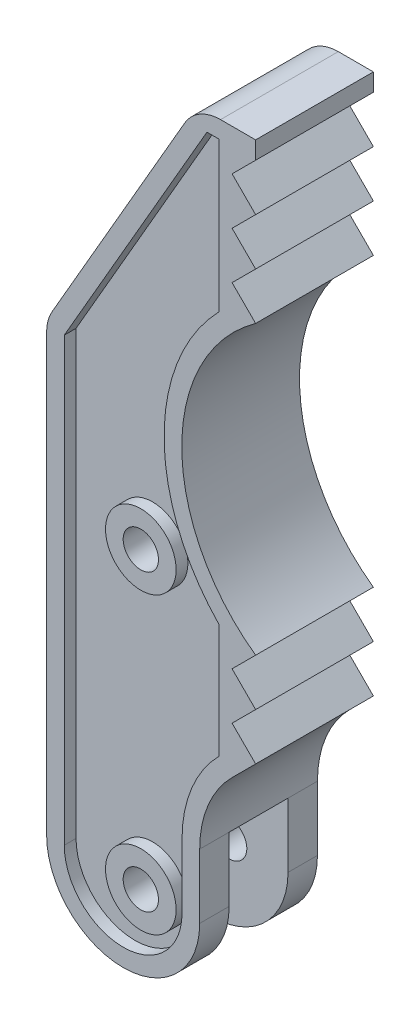
SolidWorks part; units mm, degrees
ref_plane "Front Plane" through (0, 0, 0) normal (0, 0, 1) x (1, 0, 0)
ref_plane "Top Plane" through (0, 0, 0) normal (0, 1, 0) x (1, 0, 0)
ref_plane "Right Plane" through (0, 0, 0) normal (1, 0, 0) x (0, 0, -1)
sketch "Sketch1" plane through (0, 0, 0) normal (0, 0, 1) x (1, 0, 0)
  line L0 (0, 0) -> (0, 60) construction
  line L1 (0, 60) -> (-5, 60) construction
  line L2 (-5, 60) -> (-17.75, 37.9164) construction
  line L3 (-17.75, 37.9164) -> (-17.75, 0) construction
  line L4 (-17.75, 0) -> (0, 0) construction
  line L5 (0, 58.5) -> (-2, 56.5)
  line L6 (-2, 60) -> (0, 60) construction
  line L7 (-2, 60) -> (-2, 45) construction
  line L8 (-2, 45) -> (0, 45) construction
  line L9 (0, 60) -> (0, 45) construction
  line L10 (-2, 56.5) -> (0, 54.5)
  line L11 (0, 54.5) -> (-2, 52.5)
  line L12 (-2, 52.5) -> (0, 50.5)
  line L13 (0, 50.5) -> (-2, 48.5)
  line L14 (-2, 48.5) -> (0, 46.5)
  line L15 (-17.75, 34.3) -> (0, 34.3) construction
  line L16 (-2, 20.1) -> (0, 22.1)
  line L17 (0, 18.1) -> (-2, 20.1)
  line L18 (-2, 16.1) -> (0, 18.1)
  line L19 (0, 14.1) -> (-2, 16.1)
  line L20 (-2, 12.1) -> (0, 14.1)
  line L21 (0, 58.5) -> (0, 60)
  line L22 (0, 60) -> (-5, 60)
  line L23 (-5, 60) -> (-17.75, 37.9164)
  line L24 (-17.75, 37.9164) -> (-17.75, 0)
  line L25 (-4.75, 0) -> (-4.75, 5.4609)
  line L26 (-9.75, 0) -> (-9.75, 25) construction
  arc A0 (0, 46.5) -> (0, 22.1) centre (8.727, 34.3) ccw
  arc A1 (-17.75, 0) -> (-4.75, 0) centre (-11.25, 0) ccw
  arc A2 (-4.75, 5.4609) -> (-2, 12.1) centre (4.6391, 5.4609) cw
  circle A3 centre (-9.75, 0) radius 1.5
  circle A4 centre (-9.75, 25) radius 1.5
  dimension "D10" = 15
  dimension "D11" = 6.5
  dimension "D12" = 3
  dimension "D1" = 60
  dimension "D2" = 5
  dimension "D3" = 30
  dimension "D4" = 17.75
  dimension "D5" = 2
  dimension "D6" = 15
  dimension "D7" = 1.5
  dimension "D8" = 3.5
  dimension "D9" = 24.2
  dimension "D13" = 5
  dimension "D14" = 25
extrude "Boss-Extrude1" add sketch "Sketch1" along normal mid plane 10
sketch "Sketch3" plane through (0, 0, 0) normal (0, 0, 1) x (1, 0, 0)
  line L1 (-15, -38.4108) -> (-15, -6.4108)
  line L2 (-4.75, 0) -> (-4.75, 5.4609) construction
  line L8 (-15, -38.4108) -> (-4.75, -38.4108)
  line L9 (-4.75, -38.4108) -> (-4.75, 5.4609)
  arc A2 (-15, -6.4108) -> (-4.75, 5.4609) centre (-3, -6.4108) cw
  dimension "D2" = 12
  dimension "D1" = 10.25
  dimension "D3" = 32
extrude "Cut-Extrude1" cut sketch "Sketch3" against normal mid plane 5
sketch "Sketch4" plane through (0, 0, 5) normal (0, 0, 1) x (1, 0, 0)
  line L16 (-3.1276, 58.5) -> (-3.1276, 13.0931)
  line L32 (-2.1213, 58.5) -> (-4.134, 58.5)
  line L33 (-4.134, 58.5) -> (-16.25, 37.5144)
  line L34 (-16.25, 37.5144) -> (-16.25, 0)
  line L35 (-6.25, 0) -> (-6.25, 5.4609)
  line L36 (-3.0607, 13.1607) -> (-2.1213, 14.1)
  line L37 (-2.1213, 14.1) -> (-4.1213, 16.1)
  line L38 (-4.1213, 16.1) -> (-2.1213, 18.1)
  line L39 (-2.1213, 18.1) -> (-4.1213, 20.1)
  line L40 (-4.1213, 20.1) -> (-2.2448, 21.9765)
  line L41 (-2.2448, 46.6235) -> (-4.1213, 48.5)
  line L42 (-4.1213, 48.5) -> (-2.1213, 50.5)
  line L43 (-2.1213, 50.5) -> (-4.1213, 52.5)
  line L44 (-4.1213, 52.5) -> (-2.1213, 54.5)
  line L45 (-2.1213, 54.5) -> (-4.1213, 56.5)
  line L46 (-4.1213, 56.5) -> (-2.1213, 58.5)
  line L47 (-2.1213, 58.5) -> (-4.134, 58.5)
  line L48 (-4.134, 58.5) -> (-16.25, 37.5144)
  line L49 (-16.25, 37.5144) -> (-16.25, 0)
  line L50 (-6.25, 0) -> (-6.25, 5.4609)
  line L51 (-3.0607, 13.1607) -> (-2.1213, 14.1)
  line L52 (-2.1213, 14.1) -> (-4.1213, 16.1) construction
  line L53 (-4.1213, 16.1) -> (-2.1213, 18.1) construction
  line L54 (-2.1213, 18.1) -> (-4.1213, 20.1) construction
  line L55 (-4.1213, 20.1) -> (-2.2448, 21.9765) construction
  line L56 (-2.2448, 46.6235) -> (-4.1213, 48.5) construction
  line L57 (-4.1213, 48.5) -> (-2.1213, 50.5) construction
  line L58 (-2.1213, 50.5) -> (-4.1213, 52.5) construction
  line L59 (-4.1213, 52.5) -> (-2.1213, 54.5) construction
  line L60 (-2.1213, 54.5) -> (-4.1213, 56.5) construction
  line L61 (-4.1213, 56.5) -> (-2.1213, 58.5) construction
  arc A6 (-16.25, 0) -> (-6.25, 0) centre (-11.25, 0) ccw
  arc A7 (-3.0607, 13.1607) -> (-6.25, 5.4609) centre (4.6391, 5.4609) ccw
  arc A8 (-2.2448, 46.6235) -> (-2.2448, 21.9765) centre (8.727, 34.3) ccw
  arc A9 (-16.25, 0) -> (-6.25, 0) centre (-11.25, 0) ccw
  arc A10 (-3.0607, 13.1607) -> (-6.25, 5.4609) centre (4.6391, 5.4609) ccw
  arc A11 (-2.2448, 46.6235) -> (-2.2448, 21.9765) centre (8.727, 34.3) ccw
  circle M1 centre (-9.75, 0) radius 1.5
  circle M21 centre (-9.75, 25) radius 1.5
  dimension "D1" = 1.5
extrude "Cut-Extrude2" cut sketch "Sketch4" against normal blind 1 contours A11 L16 L47 L48 L49 A9 L50 A10 M21 M1
sketch "Sketch5" plane through (0, 0, 4) normal (0, 0, 1) x (1, 0, 0)
  circle A0 centre (-9.75, 0) radius 1.5 construction
  circle A1 centre (-9.75, 25) radius 1.5 construction
  circle A2 centre (-9.75, 0) radius 1.5
  circle A3 centre (-9.75, 25) radius 1.5
extrude "Extrude-Thin1" add sketch "Sketch5" along normal blind 1 thin
fillet "Fillet1" radius 3.5 2 edges at (-5, 60, 0) (-17.75, 37.9164, 0)
